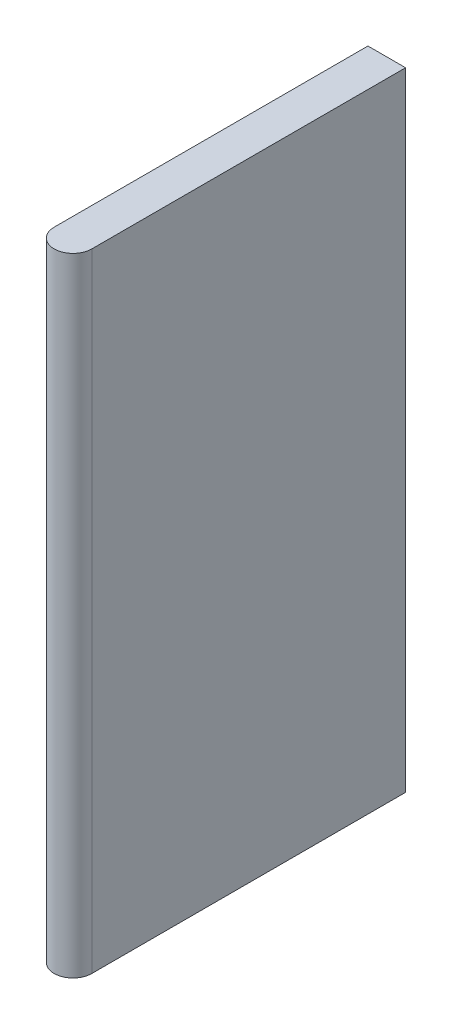
SolidWorks part; units mm, degrees
ref_plane "Front Plane" through (0, 0, 0) normal (0, 0, 1) x (1, 0, 0)
ref_plane "Top Plane" through (0, 0, 0) normal (0, 1, 0) x (1, 0, 0)
ref_plane "Right Plane" through (0, 0, 0) normal (1, 0, 0) x (0, 0, -1)
sketch "Sketch1" plane through (0, 0, 0) normal (0, 1, 0) x (1, 0, 0)
  line L2 (-0.381, -3.175) -> (-0.381, 3.175)
  line L3 (-0.381, 3.175) -> (0.381, 3.175)
  line L4 (0.381, -3.175) -> (0.381, 3.175)
  line L5 (-0.381, -3.175) -> (0.381, 3.175) construction
  line L6 (-0.381, 3.175) -> (0.381, -3.175) construction
  arc A0 (-0.381, -3.175) -> (0.381, -3.175) centre (0, -3.175) ccw
  point P1 (0, 0)
  dimension "D1" = 0.762
  dimension "D2" = 6.35
extrude "Boss-Extrude1" add sketch "Sketch1" along normal blind 12.7
